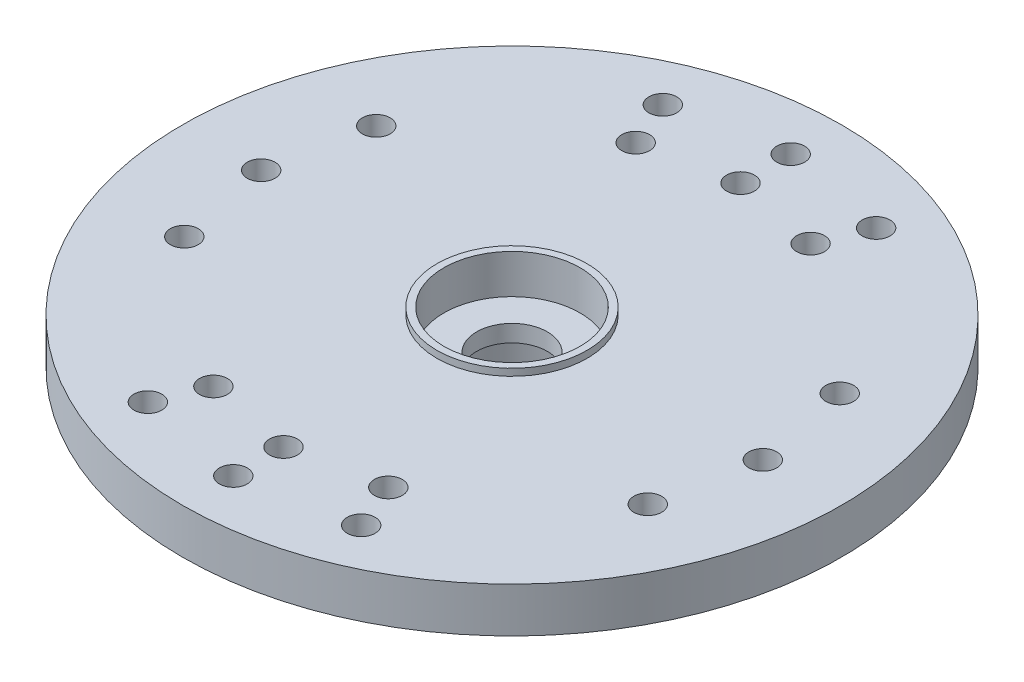
SolidWorks part; units mm, degrees
material "Nylon 101"
ref_plane "Front Plane" through (0, 0, 0) normal (0, 0, 1) x (1, 0, 0)
ref_plane "Top Plane" through (0, 0, 0) normal (0, 1, 0) x (1, 0, 0)
ref_plane "Right Plane" through (0, 0, 0) normal (1, 0, 0) x (0, 0, -1)
sketch "Sketch18" plane through (0, 0, 0) normal (0, 1, 0) x (1, 0, 0)
  circle A0 centre (0, 0) radius 11.825
  dimension "D2" = 23.65
extrude "Extrude17" add sketch "Sketch18" along normal blind 1.6129
sketch "Sketch19" plane through (0, 1.6129, 0) normal (0, 1, 0) x (1, 0, 0)
  circle A0 centre (0, 0) radius 3.4
  dimension "D1" = 6.8
extrude "Extrude19" add sketch "Sketch19" against normal blind 4.1
sketch "Sketch20" plane through (0, 1.6129, 0) normal (0, 1, 0) x (1, 0, 0)
  line L0 (-9, 0) -> (0, 0) construction
  line L1 (-8.3149, 3.4442) -> (0, 0) construction
  circle A0 centre (-9, 0) radius 0.5
  circle A1 centre (0, 0) radius 1.27
  circle A2 centre (0, 0) radius 9 construction
  circle A3 centre (-8.3149, 3.4442) radius 0.5
  circle A4 centre (-8.3149, -3.4442) radius 0.5
  dimension "D1" = 1
  dimension "D3" = 2.54
  dimension "D2" = 18
  dimension "D4" = 22.5
extrude "Extrude20" cut sketch "Sketch20" against normal through all
mirror "Mirror1" about plane through (0, 0, 0) normal (1, 0, 0) of "Extrude20"
sketch "Sketch23" plane through (0, 1.6129, 0) normal (0, 1, 0) x (1, 0, 0)
  line L0 (0, 0) -> (0, 12.2585) construction
  circle A0 centre (0, 8.2) radius 0.5
  circle A1 centre (0, 10) radius 0.5
  dimension "D3" = 1
  dimension "D1" = 8.2
  dimension "D2" = 10
extrude "Cut-Extrude1" cut sketch "Sketch23" against normal through all
pattern_circular "CirPattern1" count 2 every 22.5 about axis through (0, 0, 0) along (0, 1, 0) of "Cut-Extrude1"
mirror "Mirror2" about plane through (0, 0, 0) normal (0, 0, 1) of "CirPattern1", "Cut-Extrude1"
sketch "Sketch21" plane through (0, 1.6129, 0) normal (0, 1, 0) x (1, 0, 0)
  circle A0 centre (0, 0) radius 2.4447
  dimension "D1" = 4.8895
extrude "Extrude21" cut sketch "Sketch21" against normal blind 1.1557
sketch "Sketch22" plane through (0, -2.4871, 0) normal (0, -1, 0) x (1, 0, 0)
  circle A0 centre (0, 0) radius 2.286
  dimension "D1" = 4.572
extrude "Extrude22" cut sketch "Sketch22" against normal blind 2.3368 draft 5
sketch "Sketch24" plane through (0, 1.6129, 0) normal (0, 1, 0) x (1, 0, 0)
  circle A0 centre (0, 0) radius 2.6948
  circle A1 centre (0, 0) radius 2.4447
  circle A2 centre (0, 0) radius 2.4447
  dimension "D1" = 0
  dimension "D2" = 0.25
extrude "Boss-Extrude1" add sketch "Sketch24" along normal blind 0.25
fillet "Fillet1" radius 0.5 1 edges at (0, 0, 3.4)
